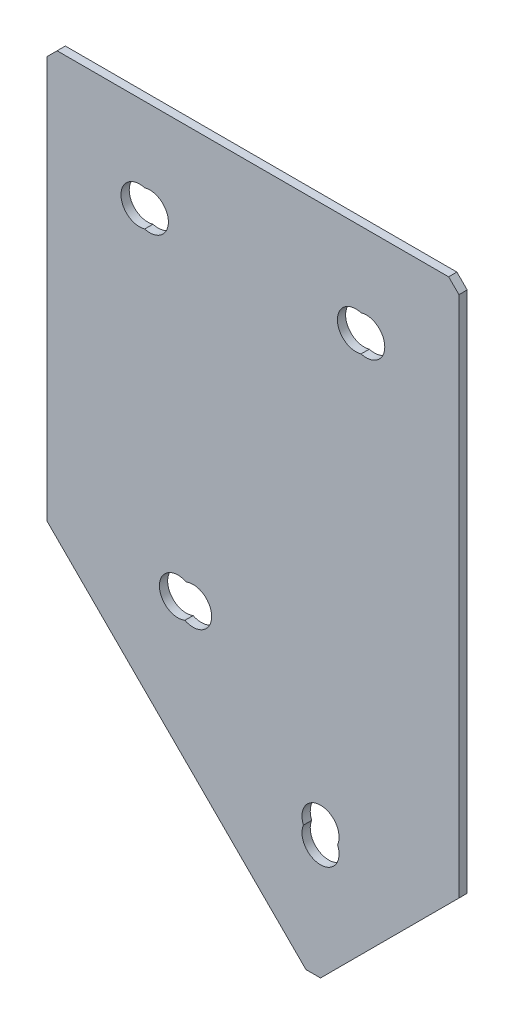
SolidWorks part; units mm, degrees
material "Простая углеродистая сталь"
ref_plane "Спереди" through (0, 0, 0) normal (0, 0, 1) x (1, 0, 0)
ref_plane "Сверху" through (0, 0, 0) normal (0, 1, 0) x (1, 0, 0)
ref_plane "Справа" through (0, 0, 0) normal (1, 0, 0) x (0, 0, -1)
sketch "Эскиз3" plane through (0, 0, 0) normal (0, 0, -1) x (1, 0, 0)
  line L0 (0, 0) -> (100, 0)
  line L1 (100, 0) -> (100, 129.2893)
  line L2 (0, 0) -> (0, 100)
  line L3 (0, 100) -> (64.6447, 164.6447)
  line L4 (64.6447, 164.6447) -> (100, 129.2893)
  dimension "D1" = 100
  dimension "D2" = 100
  dimension "D3" = 50
  dimension "D4" = 45
  dimension "D5" = 129.2893
extrude "Бобышка-Вытянуть1" add sketch "Эскиз3" along normal blind 2
hole_wizard "Отверстие с зазором M81" positions "Эскиз4" profile "Эскиз5" hole size "M8" standard "DIN" end condition through all
sketch "Эскиз4" plane through (0, 0, -2) normal (0, 0, -1) x (1, 0, 0)
  line L0 (31.8198, 100) -> (66.4124, 134.5926) construction
  line L2 (64.6447, 164.6447) -> (0, 100) construction
  line L3 (22.5, 22.5) -> (77.5, 22.5) construction
  line L5 (0, 0) -> (100, 0) construction
  line L6 (0, 100) -> (0, 0) construction
  line L7 (100, 0) -> (100, 129.2893) construction
  line L8 (100, 129.2893) -> (64.6447, 164.6447) construction
  line L9 (31.8198, 100) -> (0, 68.1802) construction
  line L10 (25, 22.5) -> (75, 22.5) construction
  line L12 (35.4968, 100.1414) -> (66.4124, 131.0571) construction
  line L13 (31.8198, 100) -> (33.5876, 98.2322) construction
  line L14 (33.5876, 98.2322) -> (35.4968, 100.1414) construction
  point P0 (22.5, 22.5)
  point P2 (77.5, 22.5)
  point P4 (31.8198, 100)
  point P6 (66.4124, 134.5926)
  point P31 (35.4968, 100.1414)
  point P33 (66.4124, 131.0571)
  point P35 (25, 22.5)
  point P37 (75, 22.5)
  dimension "D1" = 22.5
  dimension "D2" = 22.5
  dimension "D3" = 22.5
  dimension "D4" = 22.5
  dimension "D5" = 20
  dimension "D6" = 45
  dimension "D7" = 48.9214
  dimension "D8" = 55
  dimension "D9" = 22.5
  dimension "D10" = 25
  dimension "D11" = 25
  dimension "D12" = 25
  dimension "D13" = 22.5
  dimension "D14" = 2.7
sketch "Эскиз5" plane through (22.5, -22.5, -2) normal (1, 0, 0) x (0, 1, 0)
  line L0 (0, 0) -> (0, 2)
  line L1 (0, 2) -> (4.5, 2)
  line L2 (4.5, 2) -> (4.5, 0)
  line L5 (4.5, 0) -> (0, 0)
  line L11 (0, -6.35) -> (0, 107.95) construction
  dimension "Диаметр сквозного отверстия" = 9
  dimension "Глубина сквозного отверстия" = 2
chamfer "Фаска1" distance 2.5 distance2 2.5 3 edges at (64.6447, -164.6447, -1) (100, 0, -1) (0, 0, -1)
